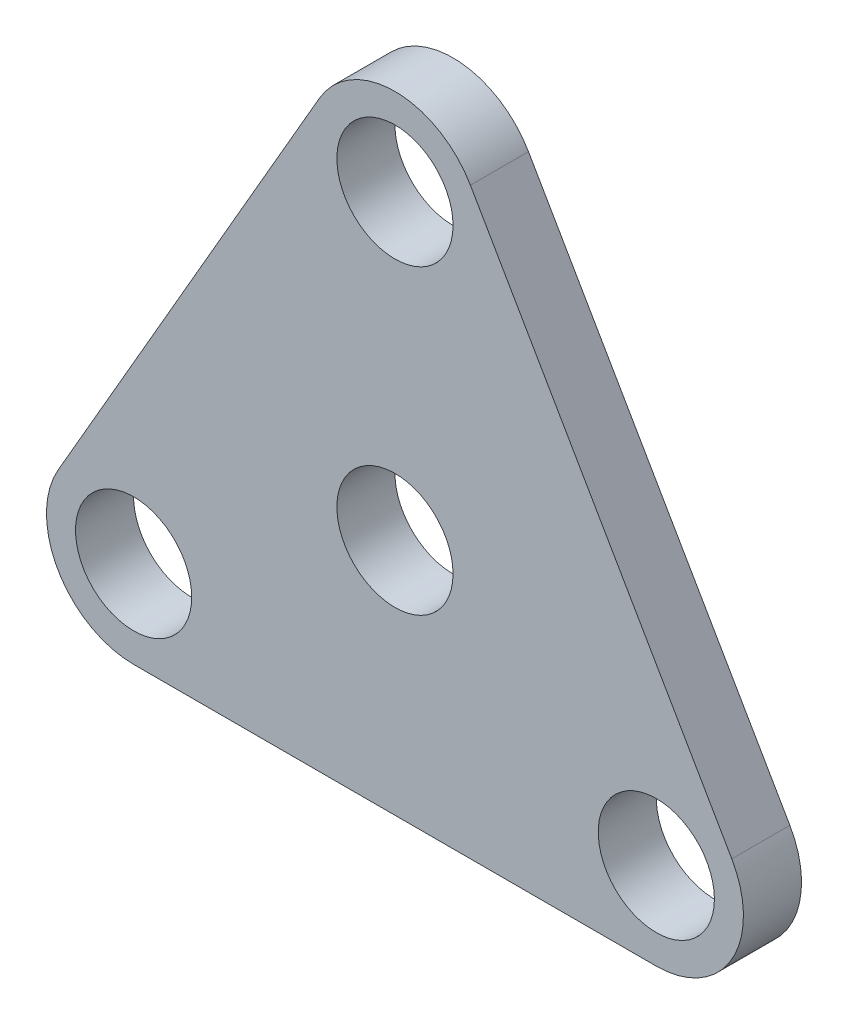
SolidWorks part; units mm, degrees
material "AISI 1020"
ref_plane "Front Plane" through (0, 0, 0) normal (0, 0, 1) x (1, 0, 0)
ref_plane "Top Plane" through (0, 0, 0) normal (0, 1, 0) x (1, 0, 0)
ref_plane "Right Plane" through (0, 0, 0) normal (1, 0, 0) x (0, 0, -1)
sketch "Sketch1" plane through (0, 0, 0) normal (0, 0, 1) x (1, 0, 0)
  line L0 (0, 13.5863) -> (0, -12.6778) construction
  line L1 (-28.575, -16.4978) -> (28.575, -16.4978) construction
  line L2 (-28.575, -16.4978) -> (0, 32.9956) construction
  line L3 (0, 32.9956) -> (28.575, -16.4978) construction
  line L4 (-9.2855, 0) -> (9.7088, 0) construction
  line L5 (14.2875, 8.2489) -> (-28.575, -16.4978) construction
  line L6 (-14.2875, 8.2489) -> (28.575, -16.4978) construction
  line L7 (-8.2489, 37.7581) -> (-36.8239, -11.7353)
  line L8 (-28.575, -26.0228) -> (28.575, -26.0228)
  line L9 (36.8239, -11.7353) -> (8.2489, 37.7581)
  circle A0 centre (0, 0) radius 6.35
  arc A1 (8.2489, 37.7581) -> (-8.2489, 37.7581) centre (0, 32.9956) ccw
  arc A2 (-36.8239, -11.7353) -> (-28.575, -26.0228) centre (-28.575, -16.4978) ccw
  arc A3 (28.575, -26.0228) -> (36.8239, -11.7353) centre (28.575, -16.4978) ccw
  circle A4 centre (-28.575, -16.4978) radius 6.35
  circle A5 centre (0, 32.9956) radius 6.35
  circle A6 centre (28.575, -16.4978) radius 6.35
  point P12 (0, 0)
  dimension "D1" = 12.7
  dimension "D3" = 19.05
  dimension "D4" = 12.7
  dimension "D2" = 57.15
extrude "Boss-Extrude1" add sketch "Sketch1" along normal blind 6.35
